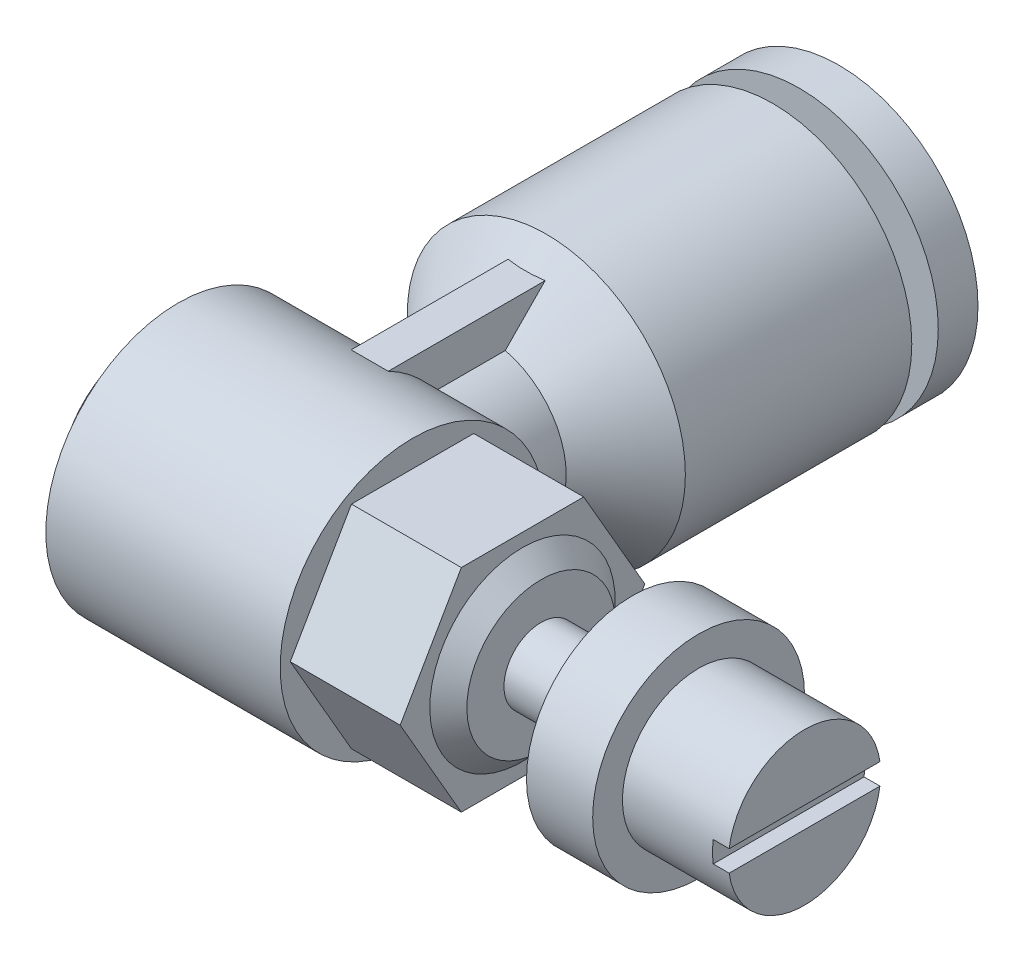
SolidWorks part; units mm, degrees
ref_plane "Front Plane" through (0, 0, 0) normal (0, 0, 1) x (1, 0, 0)
ref_plane "Top Plane" through (0, 0, 0) normal (0, 1, 0) x (1, 0, 0)
ref_plane "Right Plane" through (0, 0, 0) normal (1, 0, 0) x (0, 0, -1)
sketch "Sketch1" plane through (0, 0, 0) normal (0, 0, 1) x (1, 0, 0)
  line L0 (0, 0) -> (0, 3.125)
  line L1 (0, 3.125) -> (1.35, 3.125)
  line L2 (1.35, 3.125) -> (1.35, 5)
  line L3 (1.35, 5) -> (14.35, 5)
  line L4 (14.35, 5) -> (14.35, 3.5)
  line L5 (14.35, 3.5) -> (15.05, 2.8)
  line L6 (15.05, 2.8) -> (15.05, 1.4)
  line L7 (15.05, 1.4) -> (18.5, 1.4)
  line L8 (18.5, 1.4) -> (18.5, 4)
  line L9 (18.5, 4) -> (21, 4)
  line L10 (21, 4) -> (21, 2.875)
  line L11 (21, 2.875) -> (25, 2.875)
  line L12 (25, 2.875) -> (25, 0)
  line L13 (25, 0) -> (0, 0)
  dimension "D1" = 3.125
  dimension "D2" = 5
  dimension "D3" = 1.35
  dimension "D4" = 13
  dimension "D5" = 25
  dimension "D6" = 0.7
  dimension "D7" = 45
  dimension "D8" = 3.5
  dimension "D9" = 1.4
  dimension "D10" = 4
  dimension "D11" = 2.875
  dimension "D12" = 2.5
  dimension "D13" = 4
revolve "Revolve1" add sketch "Sketch1" angle 360 about L13
sketch "Sketch2" plane through (14.35, 0, 0) normal (1, 0, 0) x (0, 0, -1)
  line L1 (4.6188, 0) -> (2.3094, 4)
  line L2 (2.3094, 4) -> (-2.3094, 4)
  line L3 (-2.3094, 4) -> (-4.6188, 0)
  line L4 (-4.6188, 0) -> (-2.3094, -4)
  line L5 (-2.3094, -4) -> (2.3094, -4)
  line L6 (2.3094, -4) -> (4.6188, 0)
  circle A0 centre (0, 0) radius 4 construction
  dimension "D1" = 8
extrude "Cut-Extrude1" cut sketch "Sketch2" against normal blind 4.15 flip side to cut
sketch "Sketch3" plane through (25, 0, 0) normal (1, 0, 0) x (0, 0, -1)
  line L0 (-3.1922, -0.4) -> (3.1922, 0.4) construction
  line L1 (-3.1922, 0.4) -> (3.1922, 0.4)
  line L2 (-3.1922, 0.4) -> (-3.1922, -0.4)
  line L3 (-3.1922, -0.4) -> (3.1922, -0.4)
  line L4 (3.1922, 0.4) -> (3.1922, -0.4)
  dimension "D1" = 0.8
extrude "Cut-Extrude2" cut sketch "Sketch3" against normal blind 0.6
sketch "Sketch4" plane through (0, 0, 0) normal (0, 1, 0) x (1, 0, 0)
  line L0 (6.3, 0) -> (6.3, 10.9476)
  line L1 (6.3, 10.9476) -> (4.15, 10.9476)
  line L2 (4.15, 10.9476) -> (4.15, 20)
  line L3 (4.15, 20) -> (1.05, 20)
  line L4 (1.05, 20) -> (1.05, 18.5)
  line L5 (1.05, 18.5) -> (3.7, 18.5)
  line L6 (3.7, 18.5) -> (3.7, 17.5)
  line L7 (3.7, 17.5) -> (1.05, 17.5)
  line L8 (1.05, 17.5) -> (1.05, 8.95)
  line L9 (1.05, 8.95) -> (3.3, 6.7)
  line L10 (3.3, 6.7) -> (3.3, 0)
  line L11 (3.3, 0) -> (6.3, 0)
  line L12 (6.3, 0) -> (6.3, 16.5697) construction
  line L13 (0, 3.125) -> (0, -3.125) construction
  line L14 (1.35, -5) -> (10.2, -5) construction
  dimension "D1" = 4.3
  dimension "D2" = 6.3
  dimension "D3" = 6
  dimension "D4" = 45
  dimension "D5" = 10.5
  dimension "D6" = 25
  dimension "D7" = 1.5
  dimension "D8" = 5.2
  dimension "D9" = 1
  dimension "D10" = 13.3
revolve "Revolve2" add sketch "Sketch4" angle 360 about L12
sketch "Sketch5" plane through (0, 0, 0) normal (0, 0, 1) x (1, 0, 0)
  line L0 (7, -4.45) -> (5.6, 4.45) construction
  line L1 (7, 4.45) -> (5.6, 4.45)
  line L2 (7, 4.45) -> (7, -4.45)
  line L3 (7, -4.45) -> (5.6, -4.45)
  line L4 (5.6, 4.45) -> (5.6, -4.45)
  circle A0 centre (6.3, 0) radius 2.15 construction
  point P4 (6.3, 0)
  dimension "D1" = 8.9
  dimension "D2" = 1.4
extrude "Boss-Extrude1" add sketch "Sketch5" against normal blind 10
